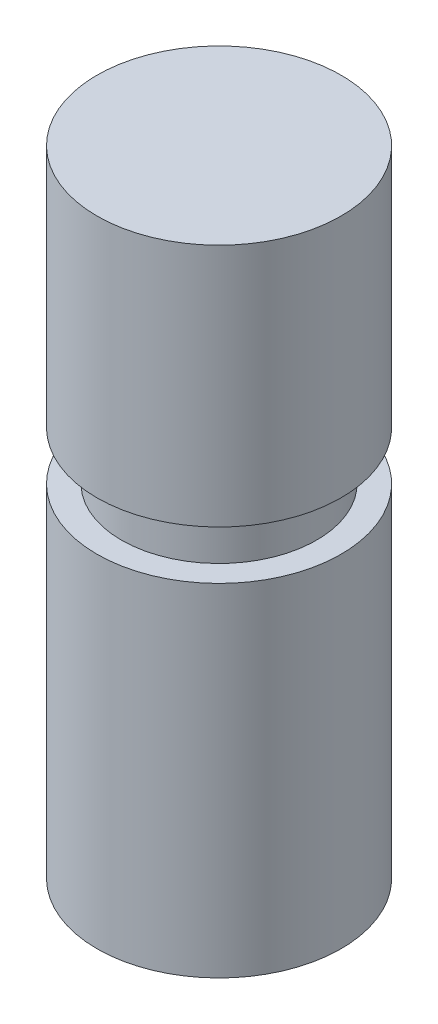
SolidWorks part; units mm, degrees
ref_plane "前视基准面" through (0, 0, 0) normal (0, 0, 1) x (1, 0, 0)
ref_plane "上视基准面" through (0, 0, 0) normal (0, 1, 0) x (1, 0, 0)
ref_plane "右视基准面" through (0, 0, 0) normal (1, 0, 0) x (0, 0, -1)
ref_plane "基准面1" through (0, 50, 0) normal (0, 1, 0) x (1, 0, 0)
ref_plane "基准面2" through (0, -10, 0) normal (0, 1, 0) x (1, 0, 0)
ref_plane "基准面3" through (0, -80, 0) normal (0, 1, 0) x (1, 0, 0)
ref_plane "基准面4" through (0, -10, 0) normal (0, 1, 0) x (1, 0, 0)
sketch "草图4" plane through (0, 50, 0) normal (0, 1, 0) x (1, 0, 0)
  circle A0 centre (0, 0) radius 25
sketch "草图5" plane through (0, -10, 0) normal (0, 1, 0) x (1, 0, 0)
  circle A0 centre (0, 0) radius 20
sketch "草图6" plane through (0, -80, 0) normal (0, 1, 0) x (1, 0, 0)
  circle A0 centre (0, 0) radius 25
extrude "凸台-拉伸1" add sketch "草图4" against normal blind 50
extrude "凸台-拉伸2" add sketch "草图5" along normal blind 50
extrude "凸台-拉伸3" add sketch "草图6" along normal blind 70 contours A0
sketch "草图8" plane through (0, 0, 0) normal (0, 0, 1) x (1, 0, 0)
  line L0 (27.5, -80) -> (-27.5, -80) construction
  line L1 (-27.5, -80) -> (-55.5, -80)
  line L3 (0, -80) -> (-27.5, -80)
  line L4 (0, 0) -> (0, -276.9201)
  line L5 (0, -276.9201) -> (0, -448.0813)
  circle A0 centre (-55.5, -80) radius 28
  point P0 (0, -80)
  point P10 (-27.5, -80)
